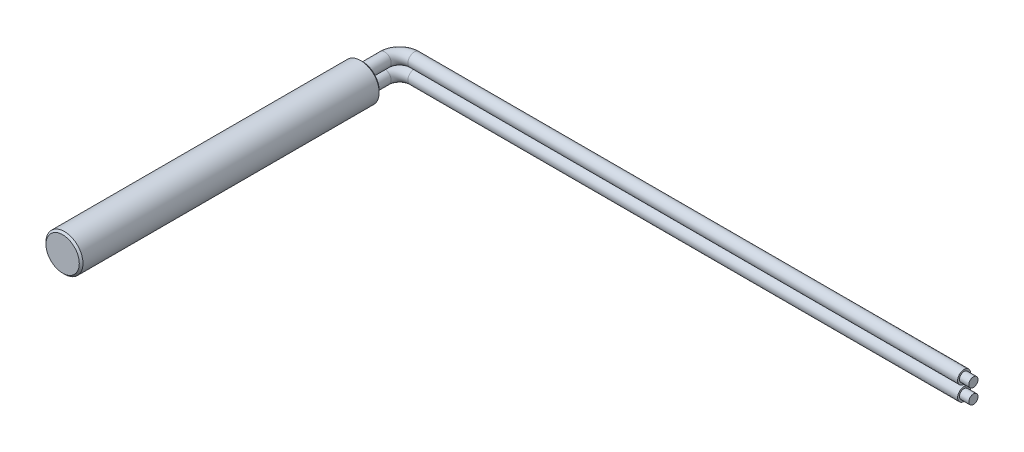
SolidWorks part; units mm, degrees
ref_plane "Front Plane" through (0, 0, 0) normal (0, 0, 1) x (1, 0, 0)
ref_plane "Top Plane" through (0, 0, 0) normal (0, 1, 0) x (1, 0, 0)
ref_plane "Right Plane" through (0, 0, 0) normal (1, 0, 0) x (0, 0, -1)
sketch "Sketch1" plane through (0, 0, 0) normal (0, 0, 1) x (1, 0, 0)
  circle A0 centre (0, 0) radius 1
  dimension "D1" = 2
extrude "Casing" add sketch "Sketch1" along normal blind 16.2
chamfer "Casing Chamfer" distance 0.1 angle 45 2 edges at (1, 0, 0) (1, 0, 16.2)
sketch "Sketch2" plane through (0, 0, 0) normal (0, 1, 0) x (1, 0, 0)
  line L0 (0, 0) -> (0, 1.2)
  line L1 (0.8, 2) -> (30.5, 2)
  arc A0 (0.8, 2) -> (0, 1.2) centre (0.8, 1.2) ccw
  point P6 (0, 2)
  dimension "D3" = 0.8
  dimension "D1" = 2
  dimension "D2" = 30.5
sketch "Sketch3" plane through (0, 0, 0) normal (0, 0, -1) x (-1, 0, 0)
  line L0 (0, 0) -> (0, 0.4) construction
  line L1 (0, 0) -> (0, -0.4) construction
  circle A1 centre (0, -0.4) radius 0.35
  circle A2 centre (0, 0.4) radius 0.35
  point P5 (-0.4993, 0)
  dimension "D2" = 0.7
  dimension "D1" = 0.8
sweep "Wire" add profiles "Sketch3" path "Sketch2"
sketch "Sketch4" plane through (30.5, 0, 0) normal (1, 0, 0) x (0, 0, -1)
  circle A2 centre (2, 0.4) radius 0.25
  circle A3 centre (2, 0.4) radius 0.25
  circle A5 centre (2, -0.4) radius 0.25
  circle A6 centre (2, -0.4) radius 0.25
  dimension "D1" = 0.1
  dimension "D2" = 0.1
extrude "Exposed Wire" add sketch "Sketch4" along normal blind 0.5
